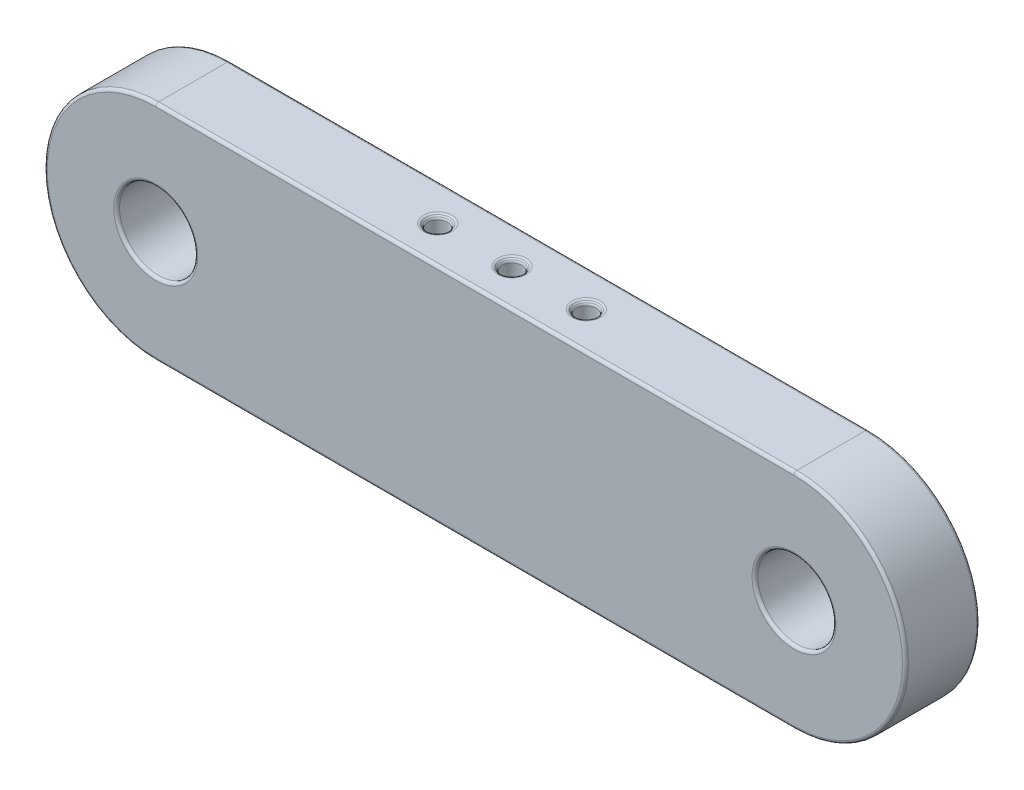
SolidWorks part; units mm, degrees
ref_plane "Front Plane" through (0, 0, 0) normal (0, 0, 1) x (1, 0, 0)
ref_plane "Top Plane" through (0, 0, 0) normal (0, 1, 0) x (1, 0, 0)
ref_plane "Right Plane" through (0, 0, 0) normal (1, 0, 0) x (0, 0, -1)
sketch "Sketch1" plane through (0, 0, 0) normal (0, 0, 1) x (1, 0, 0)
  line L0 (-42.95, 0) -> (42.95, 0) construction
  line L1 (-42.95, 15) -> (42.95, 15)
  line L2 (-42.95, -15) -> (42.95, -15)
  arc A0 (-42.95, 15) -> (-42.95, -15) centre (-42.95, 0) ccw
  arc A1 (42.95, -15) -> (42.95, 15) centre (42.95, 0) ccw
  circle A2 centre (-42.95, 0) radius 5.25
  circle A3 centre (42.95, 0) radius 5.25
  point P4 (0, 0)
  dimension "D1" = 15
  dimension "D2" = 10.5
  dimension "D3" = 85.9
extrude "Boss-Extrude1" add sketch "Sketch1" along normal blind 10
sketch "Sketch2" plane through (0, 15, 0) normal (0, 1, 0) x (1, 0, 0)
  circle A0 centre (10, -5) radius 1.35
  circle A1 centre (0, -5) radius 1.35
  circle A2 centre (-10, -5) radius 1.35
extrude "Cut-Extrude1" cut sketch "Sketch2" against normal up to next
chamfer "Chamfer1" distance 0.4 angle 45 6 edges at (-10, -15, 6.35) (0, -15, 6.35) (10, -15, 6.35) (10, 15, 6.35) (0, 15, 6.35) (-10, 15, 6.35)
fillet "Fillet1" radius 0.4 24 edges at (57.95, 0, 0) (0, -15, 0) (-57.95, 0, 0) (10, 14.6, 3.65) (10, 15, 3.25) (0, 14.6, 3.65) (0, 15, 3.25) (-10, 14.6, 3.65) (-10, 15, 3.25) (-10, -14.6, 6.35) (-10, -15, 6.75) (0, -14.6, 6.35) (0, -15, 6.75) (10, -14.6, 6.35) (10, -15, 6.75) (48.2, 0, 10) (0, 15, 10) (57.95, 0, 10) (0, -15, 10) (-57.95, 0, 10) (-37.7, 0, 10) (48.2, 0, 0) (-37.7, 0, 0) (0, 15, 0)
